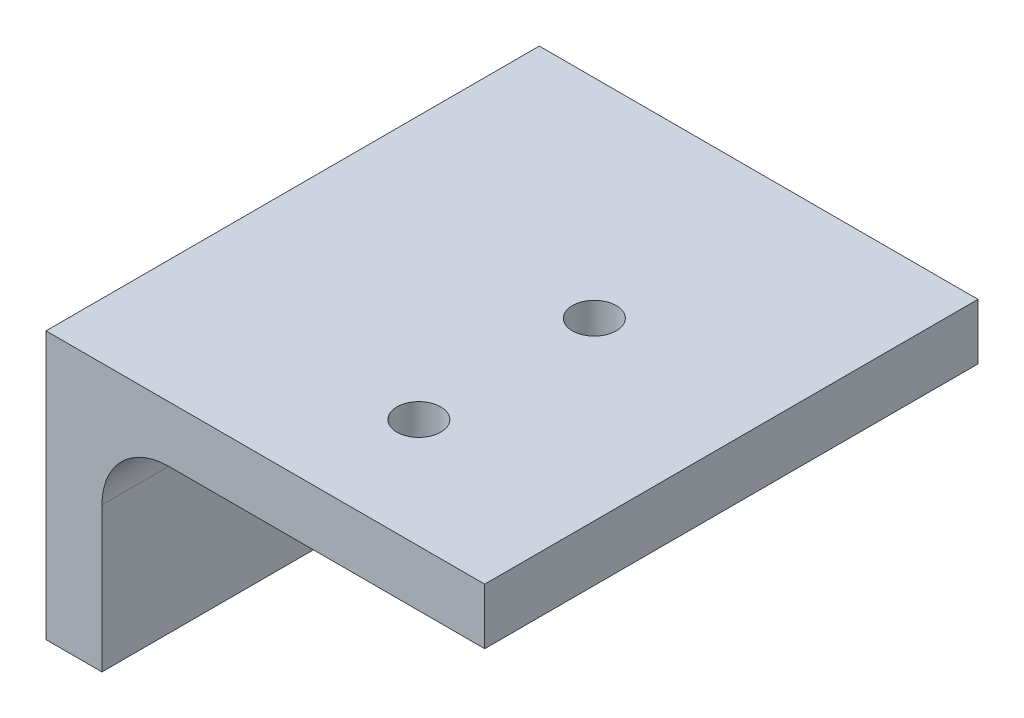
SolidWorks part; units mm, degrees
ref_plane "Front Plane" through (0, 0, 0) normal (0, 0, 1) x (1, 0, 0)
ref_plane "Top Plane" through (0, 0, 0) normal (0, 1, 0) x (1, 0, 0)
ref_plane "Right Plane" through (0, 0, 0) normal (1, 0, 0) x (0, 0, -1)
sketch "Sketch1" plane through (0, 0, 0) normal (0, 0, 1) x (1, 0, 0)
  line L0 (45.33, -9.4) -> (45.33, -39.88)
  line L1 (45.33, -39.88) -> (51.7054, -39.88)
  line L2 (51.7054, -39.88) -> (51.7054, -23.3954)
  line L3 (59.3254, -15.7754) -> (95.33, -15.7754)
  line L4 (95.33, -15.7754) -> (95.33, -9.4)
  line L5 (115, -9.4) -> (-15, -9.4) construction
  line L6 (95.33, -9.4) -> (45.33, -9.4)
  line L7 (45.33, 0) -> (45.33, 1000) construction
  arc A0 (59.3254, -15.7754) -> (51.7054, -23.3954) centre (59.3254, -23.3954) ccw
  dimension "D3" = 7.62
  dimension "D1" = 6.3754
  dimension "D2" = 6.3754
  dimension "D4" = 30.48
  dimension "D5" = 50
extrude "Boss-Extrude1" add sketch "Sketch1" against normal blind 56.22
sketch "Sketch2" plane through (0, -9.4, 0) normal (0, 1, 0) x (1, 0, 0)
  circle A0 centre (75.33, 12.4936) radius 2.5
  circle A1 centre (75.33, 32.4936) radius 2.5
extrude "Cut-Extrude1" cut sketch "Sketch2" against normal through all
sketch "Sketch4" plane through (45.33, 0, 0) normal (-1, 0, 0) x (0, 0, 1)
  line L0 (-56.22, -9.4) -> (-56.22, -39.88) construction
  line L1 (-56.22, -9.4) -> (0, -9.4) construction
  circle A0 centre (-32.598, -27.18) radius 2.5
  dimension "D2" = 5
  dimension "D1" = 23.622
  dimension "D3" = 17.78
extrude "Cut-Extrude2" cut sketch "Sketch4" against normal through all
